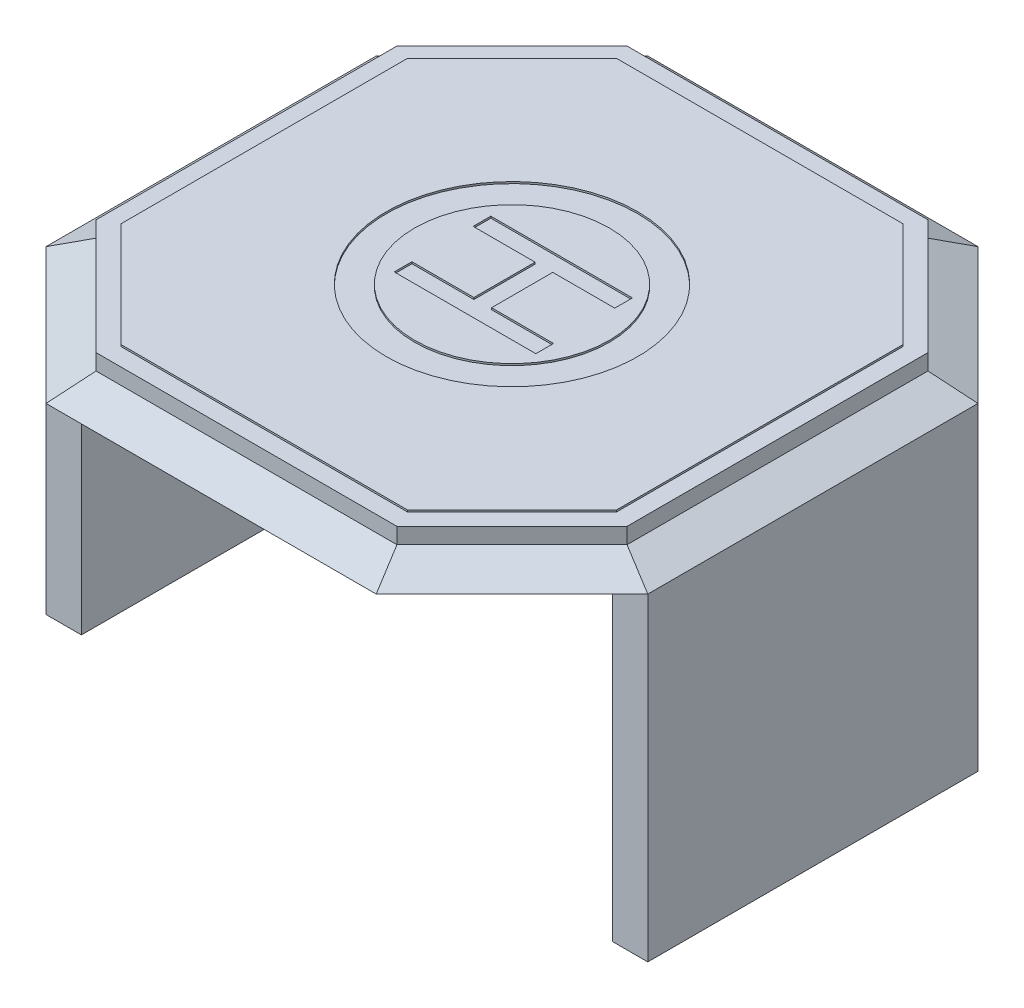
SolidWorks part; units mm, degrees
ref_plane "前视基准面" through (0, 0, 0) normal (0, 0, 1) x (1, 0, 0)
ref_plane "上视基准面" through (0, 0, 0) normal (0, 1, 0) x (1, 0, 0)
ref_plane "右视基准面" through (0, 0, 0) normal (1, 0, 0) x (0, 0, -1)
sketch "草图2" plane through (0, 0, 0) normal (0, 1, 0) x (1, 0, 0)
  line L0 (-425, 750) -> (425, 750)
  line L1 (425, 750) -> (750, 425)
  line L2 (750, 425) -> (750, -425)
  line L3 (750, -425) -> (425, -750)
  line L4 (425, -750) -> (-425, -750)
  line L5 (-425, -750) -> (-750, -425)
  line L6 (-750, -425) -> (-750, 425)
  line L7 (-750, 425) -> (-425, 750)
  dimension "D1" = 850
  dimension "D2" = 850
  dimension "D3" = 135
  dimension "D4" = 135
  dimension "D5" = 1500
  dimension "D6" = 1500
  dimension "D7" = 750
extrude "凸台-拉伸2" add sketch "草图2" along normal blind 100
sketch "草图4" plane through (0, 0, 0) normal (0, -1, 0) x (1, 0, 0)
  line L4 (-466.4214, 850) -> (466.4214, 850)
  line L8 (-850, 466.4214) -> (-466.4214, 850)
  line L12 (-850, 466.4214) -> (-850, -466.4214)
  line L16 (-850, -466.4214) -> (-466.4214, -850)
  line L20 (-466.4214, -850) -> (466.4214, -850)
  line L24 (466.4214, -850) -> (850, -466.4214)
  line L28 (850, -466.4214) -> (850, 466.4214)
  line L32 (850, 466.4214) -> (466.4214, 850)
ref_plane "基准面1" through (0, 50, 0) normal (0, 1, 0) x (1, 0, 0)
sketch "草图7" plane through (0, 50, 0) normal (0, 1, 0) x (1, 0, 0)
  line L0 (750, -425) -> (425, -750)
  line L1 (750, -425) -> (425, -750)
  line L2 (750, 425) -> (750, -425)
  line L3 (750, 425) -> (750, -425)
  line L4 (425, -750) -> (-425, -750)
  line L5 (425, -750) -> (-425, -750)
  line L6 (-425, -750) -> (-750, -425)
  line L7 (-425, -750) -> (-750, -425)
  line L8 (-750, -425) -> (-750, 425)
  line L9 (-750, -425) -> (-750, 425)
  line L10 (-750, 425) -> (-425, 750)
  line L11 (-750, 425) -> (-425, 750)
  line L12 (-425, 750) -> (425, 750)
  line L13 (-425, 750) -> (425, 750)
  line L14 (425, 750) -> (750, 425)
  line L15 (425, 750) -> (750, 425)
loft "放样4" add profiles "草图4", "草图7"
sketch "草图8" plane through (0, 100, 0) normal (0, 1, 0) x (1, 0, 0)
  circle A0 centre (0, 0) radius 355
  circle A1 centre (0, 0) radius 275
  dimension "D1" = 550
  dimension "D2" = 710
extrude "切除-拉伸1" cut sketch "草图8" against normal blind 5
sketch "草图9" plane through (0, 100, 0) normal (0, 1, 0) x (1, 0, 0)
  line L1 (-196.2605, 136.4386) -> (203.7395, 136.4386)
  line L2 (-196.2605, 136.4386) -> (-196.2605, 86.4386)
  line L3 (-196.2605, 86.4386) -> (-21.2605, 86.4386)
  line L4 (203.7395, 136.4386) -> (203.7395, 86.4386)
  line L5 (203.7395, -136.4386) -> (203.7395, -86.4386)
  line L6 (28.7395, -86.4386) -> (203.7395, -86.4386)
  line L7 (-21.2605, 86.4386) -> (-21.2605, -86.4386)
  line L8 (28.7395, 86.4386) -> (203.7395, 86.4386)
  line L9 (28.7395, 86.4386) -> (28.7395, -86.4386)
  line L10 (-196.2605, -86.4386) -> (-21.2605, -86.4386)
  line L11 (-196.2605, -136.4386) -> (-196.2605, -86.4386)
  line L12 (-196.2605, -136.4386) -> (203.7395, -136.4386)
  dimension "D1" = 50
  dimension "D3" = 400
  dimension "D4" = 175
extrude "切除-拉伸2" cut sketch "草图9" against normal blind 5
sketch "草图10" plane through (0, 100, 0) normal (0, 1, 0) x (1, 0, 0)
  line L0 (425, 750) -> (-425, 750)
  line L2 (700, 404.2893) -> (700, -404.2893)
  line L3 (700, -404.2893) -> (404.2893, -700)
  line L5 (-410.0121, 699.465) -> (-410.4228, 699.465)
  line L6 (425, 750) -> (-425, 750) construction
  line L7 (-425, 750) -> (-750, 425) construction
  line L9 (-425, 750) -> (-750, 425)
  line L10 (404.2893, -700) -> (-404.2893, -700)
  line L11 (-404.2893, -700) -> (-700, -404.2893)
  line L12 (-700, -404.2893) -> (-700, 404.2893)
  line L13 (-750, 425) -> (-750, -425)
  line L15 (-700, 404.2893) -> (-404.2893, 700)
  line L16 (-404.2893, 700) -> (404.2893, 700)
  line L17 (404.2893, 700) -> (700, 404.2893)
  line L18 (-750, -425) -> (-425, -750)
  line L22 (-425, -750) -> (425, -750)
  line L26 (-425, -750) -> (425, -750) construction
  line L27 (425, -750) -> (750, -425)
  line L31 (750, -425) -> (750, 425)
  line L34 (694.2772, 480.7228) -> (694.2772, 699.465)
  line L35 (750, 425) -> (425, 750)
  dimension "D1" = 50
  dimension "D2" = 50
  dimension "D3" = 50
  dimension "D4" = 50
  dimension "D5" = 50
  dimension "D7" = 50
  dimension "D8" = 50
  dimension "D9" = 50
extrude "切除-拉伸3" cut sketch "草图10" against normal blind 5
sketch "草图13" plane through (0, 0, 0) normal (0, -1, 0) x (1, 0, 0)
  line L0 (-850, 466.4214) -> (-850, -466.4214)
  line L1 (-850, 466.4214) -> (-750, 466.4214)
  line L2 (-850, -466.4214) -> (-750, -466.4214)
  line L3 (-750, 466.4214) -> (-750, -466.4214)
  line L4 (850, -466.4214) -> (850, 466.4214)
  line L5 (850, -466.4214) -> (750, -466.4214)
  line L6 (850, 466.4214) -> (750, 466.4214)
  line L7 (750, -466.4214) -> (750, 466.4214)
  dimension "D1" = 100
  dimension "D2" = 100
extrude "凸台-拉伸3" add sketch "草图13" along normal blind 900
sketch "草图12" plane through (0, 100, 0) normal (0, 1, 0) x (1, 0, 0)
